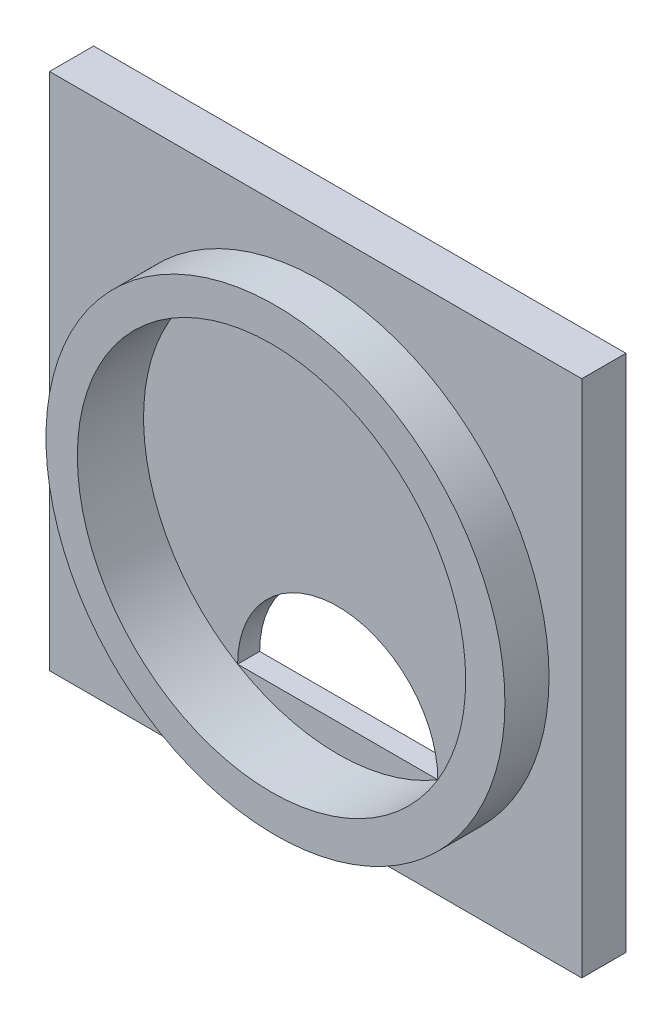
SolidWorks part; units mm, degrees
material "ABS"
ref_plane "Front Plane" through (0, 0, 0) normal (0, 0, 1) x (1, 0, 0)
ref_plane "Top Plane" through (0, 0, 0) normal (0, 1, 0) x (1, 0, 0)
ref_plane "Right Plane" through (0, 0, 0) normal (1, 0, 0) x (0, 0, -1)
sketch "Sketch16" plane through (0, 0, 0) normal (0, 0, 1) x (1, 0, 0)
  line L6 (-30.15, 31.15) -> (30.15, 31.15)
  line L11 (-30.15, 31.15) -> (-30.15, -27.65)
  line L12 (-30.15, -27.65) -> (30.15, -27.65)
  line L13 (30.15, 31.15) -> (30.15, -27.65)
  circle A0 centre (0, 0) radius 22
extrude "Boss-Extrude2" add sketch "Sketch16" against normal blind 5
sketch "Sketch22" plane through (0, 31.15, 0) normal (0, 1, 0) x (1, 0, 0)
  line L0 (30.15, 5) -> (30.15, 2.5)
  line L1 (30.15, 5) -> (30.15, 0) construction
  line L2 (30.15, 2.5) -> (-30.15, 2.5)
  line L3 (-30.15, 5) -> (-30.15, 0) construction
  line L4 (-30.15, 2.5) -> (-30.15, 5)
  line L5 (-30.15, 5) -> (30.15, 5)
extrude "Boss-Extrude7" add sketch "Sketch22" against normal blind 50
sketch "Sketch23" plane through (0, 0, 0) normal (0, 0, 1) x (1, 0, 0)
  circle A0 centre (0, 0) radius 22
  circle A1 centre (0.4439, 0) radius 26
extrude "Boss-Extrude8" add sketch "Sketch23" along normal blind 5
sketch "Sketch24" plane through (0, 0, -2.5) normal (0, 0, 1) x (1, 0, 0)
  line L1 (-11.3436, -18.85) -> (11.3436, -18.85) construction
  line L2 (-11.3436, -18.85) -> (11.3436, -18.85)
  arc A0 (11.3436, -18.85) -> (-11.3436, -18.85) centre (0, 0) ccw construction
  arc A1 (-11.3436, -18.85) -> (11.3436, -18.85) centre (0, -18.85) cw
extrude "Cut-Extrude3" cut sketch "Sketch24" against normal up to surface (2.5 mm away) up to face at (0, -20.425, -5)
sketch "Sketch25" plane through (0, 0, -2.5) normal (0, 0, 1) x (1, 0, 0)
  line L3 (-11.3436, -18.85) -> (11.3436, -18.85)
  arc A0 (-11.3436, -18.85) -> (11.3436, -18.85) centre (0, 0) ccw
  arc A1 (11.3436, -18.85) -> (-11.3436, -18.85) centre (0, -18.85) ccw construction
extrude "Boss-Extrude9" add sketch "Sketch25" against normal up to surface (2.5 mm away) up to face at (0, -14.7532, -5)
